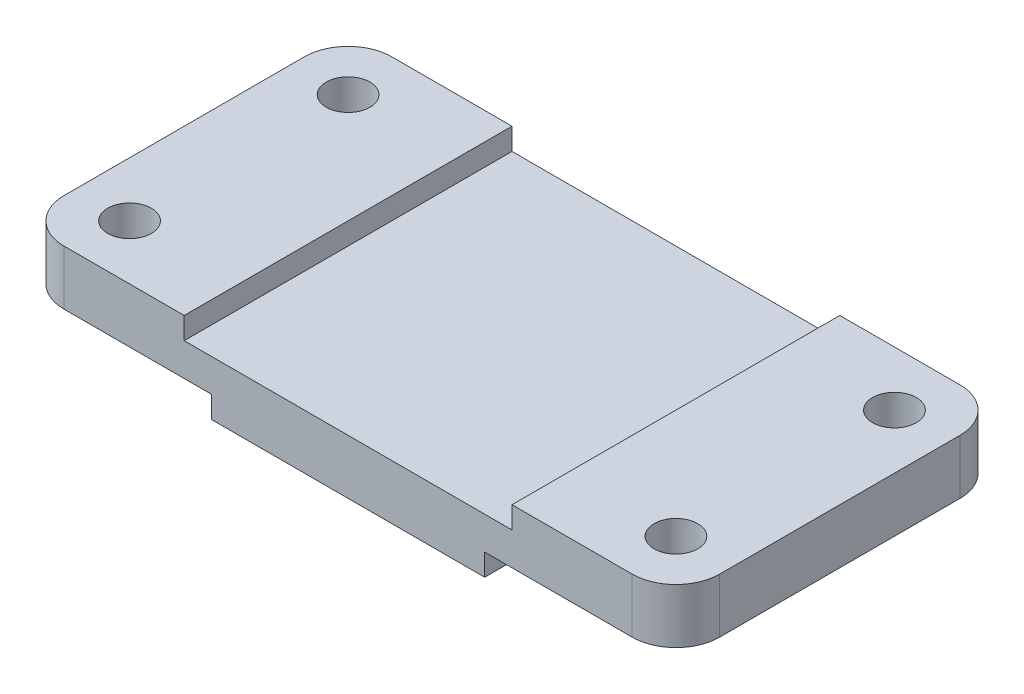
SolidWorks part; units mm, degrees
ref_plane "Front Plane" through (0, 0, 0) normal (0, 0, 1) x (1, 0, 0)
ref_plane "Top Plane" through (0, 0, 0) normal (0, 1, 0) x (1, 0, 0)
ref_plane "Right Plane" through (0, 0, 0) normal (1, 0, 0) x (0, 0, -1)
sketch "Sketch1" plane through (0, 0, 0) normal (0, 1, 0) x (1, 0, 0)
  line L0 (76.2, 0) -> (0, 0)
  line L1 (0, 0) -> (0, 38.1)
  line L2 (0, 38.1) -> (76.2, 38.1)
  line L3 (76.2, 38.1) -> (76.2, 0)
  dimension "D1" = 76.2
  dimension "D2" = 38.1
extrude "Boss-Extrude3" add sketch "Sketch1" along normal blind 6.35
sketch "Sketch3" plane through (0, 6.35, 0) normal (0, 1, 0) x (1, 0, 0)
  line L0 (19.05, 0) -> (19.05, 38.1)
  line L1 (0, 0) -> (76.2, 0) construction
  line L2 (76.2, 38.1) -> (0, 38.1) construction
  line L3 (19.05, 38.1) -> (57.15, 38.1)
  line L4 (57.15, 38.1) -> (57.15, 0)
  line L5 (57.15, 0) -> (19.05, 0)
  dimension "D1" = 38.1
  dimension "D2" = 19.05
  dimension "D3" = 19.05
extrude "Cut-Extrude1" cut sketch "Sketch3" against normal blind 2.54 contours L0 L3 L4 L5
sketch "Sketch4" plane through (0, 0, 0) normal (0, -1, 0) x (1, 0, 0)
  line L0 (22.225, 0) -> (22.225, -38.1)
  line L1 (0, 0) -> (76.2, 0) construction
  line L2 (76.2, -38.1) -> (0, -38.1) construction
  line L3 (22.225, -38.1) -> (53.975, -38.1)
  line L4 (53.975, -38.1) -> (53.975, 0)
  line L5 (53.975, 0) -> (22.225, 0)
  dimension "D1" = 31.75
  dimension "D2" = 22.225
  dimension "D3" = 22.225
extrude "Boss-Extrude4" add sketch "Sketch4" along normal blind 2.54
sketch "Sketch5" plane through (0, 3.81, 0) normal (0, 1, 0) x (1, 0, 0)
  circle A0 centre (6.35, 31.75) radius 2.54
  circle A1 centre (6.35, 6.35) radius 2.54
  circle A2 centre (69.85, 31.75) radius 2.54
  circle A3 centre (69.85, 6.35) radius 2.54
  dimension "D1" = 5.08
  dimension "D4" = 5.08
  dimension "D7" = 5.08
  dimension "D10" = 5.08
  dimension "D2" = 6.35
  dimension "D3" = 31.75
  dimension "D5" = 6.35
  dimension "D6" = 31.75
  dimension "D8" = 6.35
  dimension "D9" = 31.75
  dimension "D11" = 6.35
  dimension "D12" = 31.75
extrude "Cut-Extrude5" cut sketch "Sketch5" along normal blind 6.35 and the other way blind 6.35
fillet "Fillet1" radius 5.08 4 edges at (0, 3.175, -38.1) (0, 3.175, 0) (76.2, 3.175, 0) (76.2, 3.175, -38.1)
